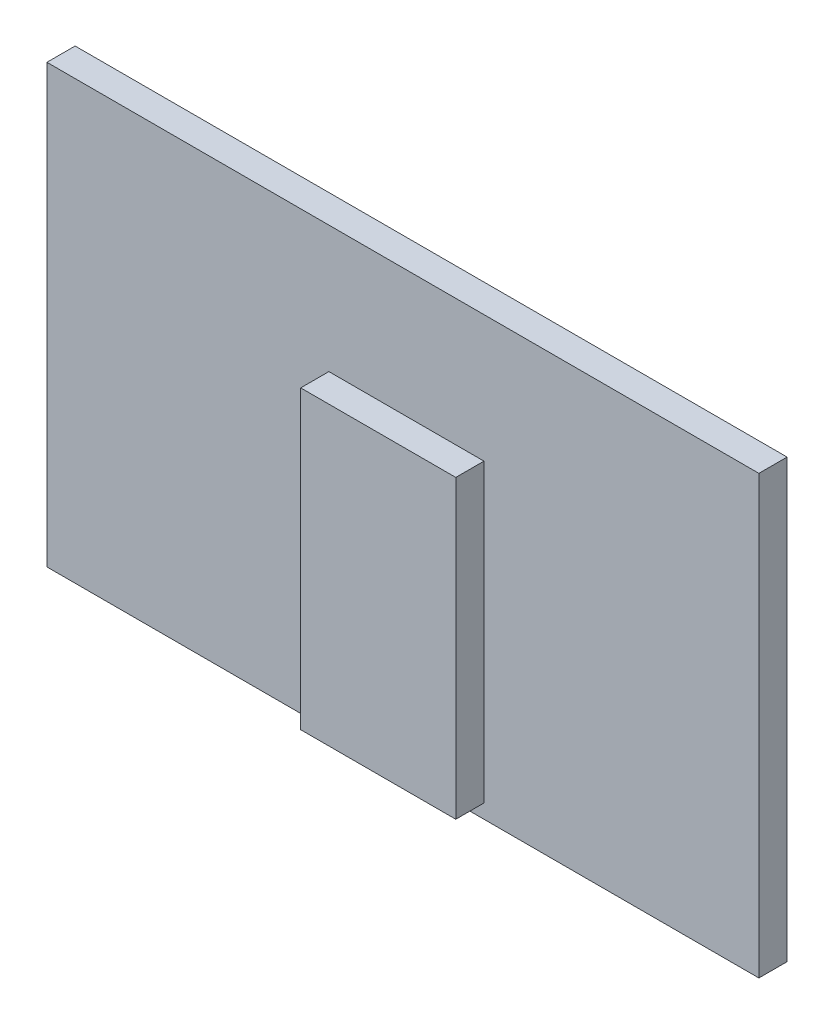
SolidWorks part; units mm, degrees
ref_plane "Płaszczyzna przednia" through (0, 0, 0) normal (0, 0, 1) x (1, 0, 0)
ref_plane "Płaszczyzna górna" through (0, 0, 0) normal (0, 1, 0) x (1, 0, 0)
ref_plane "Płaszczyzna prawa" through (0, 0, 0) normal (1, 0, 0) x (0, 0, -1)
sketch "Szkic1" plane through (0, 0, 0) normal (0, 0, 1) x (1, 0, 0)
  line L1 (-332.9275, 178.25) -> (172.0725, 178.25)
  line L2 (-332.9275, 178.25) -> (-332.9275, -131.75)
  line L3 (-332.9275, -131.75) -> (172.0725, -131.75)
  line L4 (172.0725, 178.25) -> (172.0725, -131.75)
  dimension "D1" = 310
  dimension "D2" = 505
extrude "Dodanie-wyciągnięcie1" add sketch "Szkic1" along normal blind 20
sketch "Szkic2" plane through (0, 0, 20) normal (0, 0, 1) x (1, 0, 0)
  line L0 (-332.9275, -131.75) -> (172.0725, -131.75) construction
  line L1 (-132.9275, 88.25) -> (-22.9275, 88.25)
  line L2 (-132.9275, 88.25) -> (-132.9275, -121.75)
  line L3 (-132.9275, -121.75) -> (-22.9275, -121.75)
  line L4 (-22.9275, 88.25) -> (-22.9275, -121.75)
  line L5 (-332.9275, 178.25) -> (-332.9275, -131.75) construction
  dimension "D1" = 110
  dimension "D2" = 210
  dimension "D3" = 10
  dimension "D4" = 200
extrude "Dodanie-wyciągnięcie2" add sketch "Szkic2" along normal blind 20
